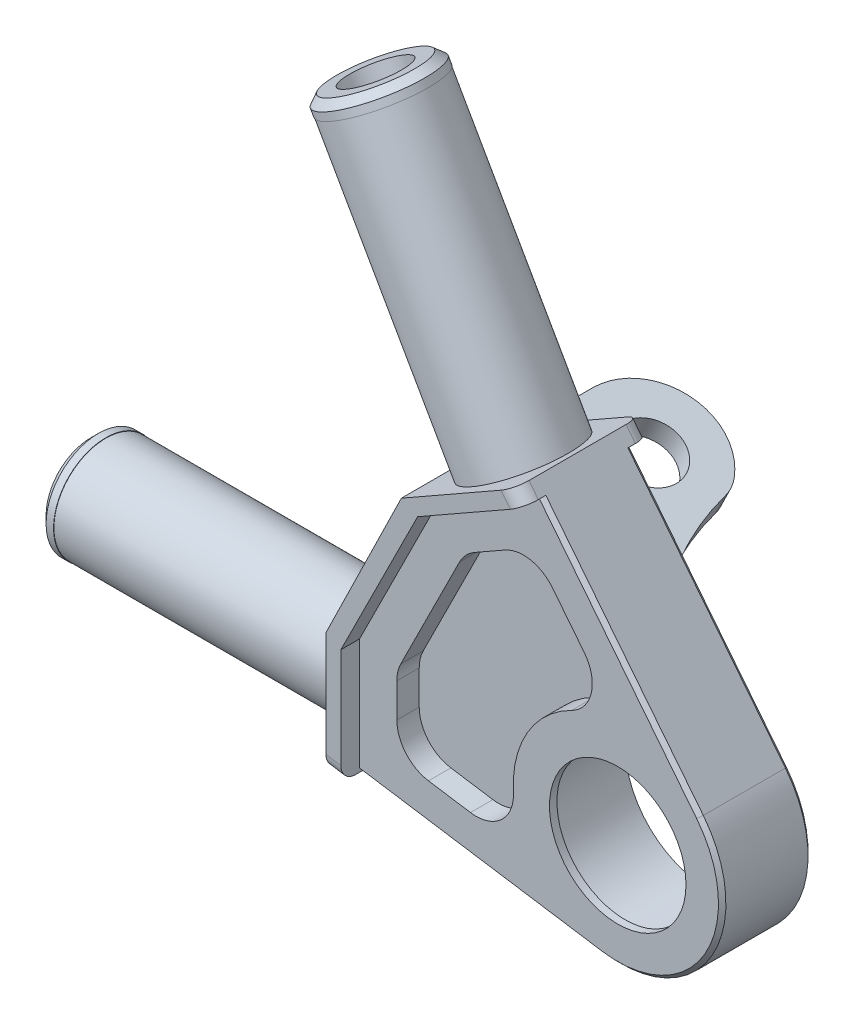
SolidWorks part; units mm, degrees
material "7075-T6 (SN)"
ref_plane "Płaszczyzna XY" through (0, 0, 0) normal (0, 0, 1) x (1, 0, 0)
ref_plane "Płaszczyzna XZ" through (0, 0, 0) normal (0, 1, 0) x (1, 0, 0)
ref_plane "Płaszczyzna YZ" through (0, 0, 0) normal (1, 0, 0) x (0, 0, -1)
sketch3d "Szkic 3D3"
  line L2 (-29.2958, 16.8586, -11.1226) -> (-29.2958, 16.8586, 0) construction
  line L3 (-9.7916, 7.3154, 0) -> (-29.2958, 16.8586, 0) construction
ref_plane "Płaszczyzna2" through (0.9966, 2.0369, 0) normal (0.4395, 0.8982, 0) x (0.8982, -0.4395, 0)
sketch "Szkic1" plane through (0, 0, 0) normal (0, 0, 1) x (1, 0, 0)
  line L0 (0, 0) -> (-69.9038, 0) construction
  line L1 (0, 0) -> (-41.2537, 72.4391) construction
  line L2 (-40, -8) -> (-2.1327, -13.8366)
  line L3 (-40, -8) -> (-40, 8)
  line L4 (-26.7466, 30.7997) -> (-12.8431, 38.7176)
  line L5 (-12.8431, 38.7176) -> (10.9681, 8.7006)
  line L9 (-26.7466, 30.7997) -> (-40, 8)
  circle A0 centre (0, 0) radius 11
  arc A1 (-2.1327, -13.8366) -> (10.9681, 8.7006) centre (0, 0) ccw
  dimension "D1" = 3
  dimension "D2" = 22
  dimension "D3" = 60.339
  dimension "D4" = 8
  dimension "D5" = 8
  dimension "D6" = 40
  dimension "D7" = 40
  dimension "D8" = 8
  dimension "D9" = 8
extrude "Dodanie-wyciągnięcie1" add sketch "Szkic1" along normal blind 12
sketch "Szkic4" plane through (0, 0, 12) normal (0, 0, 1) x (1, 0, 0)
  circle A0 centre (0, 0) radius 11.1475
  circle A1 centre (0, 0) radius 9.1475
  dimension "D1" = 2
extrude "Dodanie-wyciągnięcie2" add sketch "Szkic4" against normal blind 1
sketch "Szkic13" plane through (0.9966, 2.0369, 0) normal (0.4395, 0.8982, 0) x (0.8982, -0.4395, 0)
  line L0 (-36.2241, 11.1226) -> (-36.2241, 0)
  line L1 (-36.2241, 0) -> (-33.7241, 0)
  line L2 (-13.2241, 0) -> (-33.7241, 0)
  arc A0 (-20.3744, 15.3924) -> (-36.2241, 11.1226) centre (-27.7241, 11.1226) ccw
  arc A1 (-13.2241, 0) -> (-20.3744, 15.3924) centre (12.2627, 21.1964) cw
  circle A4 centre (-27.7241, 11.1226) radius 4
  dimension "D1" = 17
  dimension "D2" = 33.1492
  dimension "D3" = 23
  dimension "D4" = 15.3924
extrude "Dodanie-wyciągnięcie3" add sketch "Szkic13" along normal mid plane 23
ref_plane "Płaszczyzna3" through (0, 0, 6) normal (0, 0, -1) x (-1, 0, 0)
sketch "Szkic15" plane through (0, 0, 0) normal (0, 0, -1) x (-1, 0, 0)
  line L0 (12.8431, 38.7176) -> (26.7466, 30.7997)
  line L1 (26.7466, 30.7997) -> (40, 8)
  line L2 (40, 8) -> (40, -8)
  line L3 (12.0981, 37.4094) -> (11.8965, 37.5242)
  line L4 (12.8431, 38.7176) -> (11.8965, 37.5242)
  line L5 (40, -8) -> (38.4945, -8.232)
  line L7 (40, -8) -> (2.1327, -13.8366) construction
  line L8 (38.4945, 8) -> (38.4945, -8.232)
  line L10 (38.4945, 8) -> (26.0016, 29.4914)
  line L11 (26.0016, 29.4914) -> (12.0981, 37.4094)
  dimension "D1" = 1.5233
  dimension "D2" = 16
  dimension "D3" = 0.232
  dimension "D4" = 24.8587
  dimension "D5" = 16.232
extrude "Wytnij-wyciągnięcie1" cut sketch "Szkic15" against normal through all
sketch "Szkic16" plane through (0, 0, 0) normal (0, 0, -1) x (-1, 0, 0)
  line L1 (26.4872, 28.2872) -> (36.5957, 7.6276)
  line L2 (26.4872, 28.2872) -> (11.3895, 36.8852)
  line L3 (11.8965, 37.5242) -> (11.3895, 36.8852)
  line L4 (-10.9681, 8.7006) -> (11.8965, 37.5242) construction
  line L5 (11.8965, 37.5242) -> (26.0016, 29.4914)
  line L6 (26.0016, 29.4914) -> (38.4945, 8)
  line L7 (38.4945, 8) -> (38.4945, -8.232)
  line L10 (36.5957, 7.6276) -> (36.5957, -8.5247)
  line L11 (38.4945, -8.232) -> (36.5957, -8.5247)
  dimension "D1" = 1.9212
extrude "Wytnij-wyciągnięcie2" cut sketch "Szkic16" against normal through all
sketch "Szkic17" plane through (-32.5381, 15.9205, 0) normal (-0.8982, 0.4395, 0) x (0, 0, 1)
  line L2 (-27.8142, 10.7676) -> (-27.8142, -7.2324)
  line L4 (-27.8142, 10.7676) -> (0, 10.7676)
  line L5 (-27.8142, -7.2324) -> (0, -7.2324)
  line L6 (0, -7.2324) -> (2.5, -7.2324)
  line L7 (2.5, -7.2324) -> (2.5, 10.7676)
  line L8 (2.5, 10.7676) -> (0, 10.7676)
  line L10 (-11.1226, 13.7676) -> (0, 13.7676) construction
  line L11 (12, 13.7676) -> (12, -9.2324) construction
  dimension "D1" = 18
  dimension "D2" = 3
  dimension "D3" = 2.5
  dimension "D4" = 30.3142
  dimension "D5" = 9.5
extrude "Wytnij-wyciągnięcie3" cut sketch "Szkic17" against normal up to vertex (23 mm away)
sketch "Szkic18" plane through (0, 0, 6) normal (0, 0, -1) x (-1, 0, 0)
  line L0 (0, 0) -> (76.5957, 0) construction
  line L2 (76.5957, 0) -> (76.5957, -7)
  line L3 (76.5957, -7) -> (74.5957, -7)
  line L4 (74.5957, -7) -> (74.5957, -6.95)
  line L8 (74.5957, -6.95) -> (36.5957, -6.95)
  line L9 (36.5957, 7.6276) -> (36.5957, -8.5247) construction
  line L10 (36.5957, -6.95) -> (36.5957, 0)
  line L11 (36.5957, 0) -> (76.5957, 0)
  dimension "D1" = 40
  dimension "D2" = 7
  dimension "D3" = 2
  dimension "D4" = 6.95
revolve "Obrót1" add sketch "Szkic18" angle 360 about L0
sketch "Szkic19" plane through (0, 0, 6) normal (0, 0, -1) x (-1, 0, 0)
  line L0 (0, 0) -> (38.4457, 67.5085) construction
  line L1 (11.3895, 36.8852) -> (26.4872, 28.2872) construction
  line L2 (38.4457, 67.5085) -> (32.363, 70.9726)
  line L3 (32.363, 70.9726) -> (31.3732, 69.2347)
  line L4 (31.3732, 69.2347) -> (31.4167, 69.21)
  line L5 (31.4167, 69.21) -> (12.6116, 36.1893)
  line L6 (12.6116, 36.1893) -> (18.6509, 32.7499)
  line L7 (18.6509, 32.7499) -> (38.4457, 67.5085)
  dimension "D1" = 40
  dimension "D2" = 90
  dimension "D3" = 7
  dimension "D4" = 2
  dimension "D5" = 6.95
  dimension "D6" = 40
  dimension "D7" = 6.95
revolve "Obrót2" add sketch "Szkic19" angle 360 about L0
sketch "Szkic20" plane through (0, 0, 0) normal (0, 0, -1) x (-1, 0, 0)
  line L1 (36.5957, -8.5247) -> (34.5957, -8.833)
  line L2 (36.5957, -8.5247) -> (2.1327, -13.8366) construction
  line L4 (36.5957, 7.6276) -> (15.9361, -2.4809) construction
  line L5 (34.5957, 6.649) -> (36.5957, 7.6276)
  line L6 (26.4872, 28.2872) -> (11.3895, 36.8852)
  line L7 (11.3895, 36.8852) -> (10.1319, 35.2998)
  line L8 (-10.9681, 8.7006) -> (11.3895, 36.8852) construction
  line L9 (10.1319, 35.2998) -> (24.3134, 27.2235)
  line L10 (26.4872, 28.2872) -> (12.2503, 21.3212) construction
  line L11 (24.3134, 27.2235) -> (26.4872, 28.2872)
  line L12 (36.5957, 7.6276) -> (36.5957, -8.5247)
  line L13 (34.5957, -8.833) -> (34.5957, 6.649)
  dimension "D1" = 2
  dimension "D2" = 2
extrude "Dodanie-wyciągnięcie4" add sketch "Szkic20" along normal blind 2.5 and the other way blind 14.5
sketch "Szkic21" plane through (0, 0, 12) normal (0, 0, 1) x (1, 0, 0)
  line L3 (-24.3134, 27.2235) -> (-26.4872, 28.2872)
  line L4 (-24.3134, 27.2235) -> (-34.5957, 6.649)
  line L5 (-34.5957, 6.649) -> (-36.5957, 7.6276)
  line L6 (-36.5957, 7.6276) -> (-26.4872, 28.2872)
extrude "Dodanie-wyciągnięcie5" add sketch "Szkic21" along normal blind 2.5
hole_wizard "Otwory ustalające Ø8.0mm1" positions "Szkic 3D4" profile "Szkic22" hole size "Ø8.0" standard "ISO"
sketch3d "Szkic 3D4"
  line L0 (-76.5957, 0, 6) -> (-74.5957, 0, 6) construction
  point P0 (-76.5957, 0, 6)
sketch "Szkic22" plane through (-76.5957, 0, 6) normal (0, 1, 0) x (0, 0, 1)
  line L0 (0, 0) -> (0, 42.4034)
  line L1 (0, 42.4034) -> (4, 40)
  line L2 (4, 40) -> (4, 0)
  line L5 (4, 0) -> (0, 0)
  line L10 (0, 42.4034) -> (-4, 40) construction
  line L11 (0, -6.35) -> (0, 107.95) construction
  dimension "Średnica otworu" = 8
  dimension "Głębokość otworu" = 40
  dimension "Kąt wiertła" = 118
hole_wizard "Otwory ustalające Ø8.0mm2" positions "Szkic 3D5" profile "Szkic23" hole size "Ø8.0" standard "ISO"
sketch3d "Szkic 3D5"
  line L0 (-38.4457, 67.5085, 6) -> (-37.456, 65.7706, 6) construction
  point P0 (-38.4457, 67.5085, 6)
sketch "Szkic23" plane through (-38.4457, 67.5085, 6) normal (0, 0, 1) x (-0.869, -0.4949, 0)
  line L0 (0, 0) -> (0, 42.4034)
  line L1 (0, 42.4034) -> (4, 40)
  line L2 (4, 40) -> (4, 0)
  line L5 (4, 0) -> (0, 0)
  line L10 (0, 42.4034) -> (-4, 40) construction
  line L11 (0, -6.35) -> (0, 107.95) construction
  dimension "Średnica otworu" = 8
  dimension "Głębokość otworu" = 40
  dimension "Kąt wiertła" = 118
chamfer "Sfazowanie1" distance 1 angle 45 2 edges at (-32.363, 70.9726, 6) (-76.5957, 0, -1)
fillet "Zaokrąglenie2" radius 2 4 edges at (-10.7607, 36.0925, -2.5) (-10.7607, 36.0925, 14.5) (-35.5957, -8.6788, 14.5) (-35.5957, -8.6788, -2.5)
fillet "Zaokrąglenie3" radius 5 4 edges at (-24.3134, 27.2235, -1.25) (-15.0571, -0.6844, 1.25) (-7.1461, 15.4839, 1.25) (-34.5957, 6.649, -1.25)
chamfer "Sfazowanie2" distance 0.5 angle 45 6 edges at (-18.3642, -11.3348, 0) (-18.3642, -11.3348, 12) (12.1036, -7.0358, 0) (12.1036, -7.0358, 12) (0.4181, 22.0002, 12) (0.4181, 22.0002, 0)
fillet "Zaokrąglenie4" radius 0.3 1 edges at (11, 0, 11)
sketch "Szkic24" plane through (6.0509, 12.3667, 0) normal (0.4395, 0.8982, 0) x (0.8982, -0.4395, 0)
  line L0 (-27.7241, 11.1226) -> (-3.3355, 11.1226) construction
  line L2 (-27.7241, 11.1226) -> (-19.5533, -3.0985) construction
  dimension "D1" = 60.12
fillet "Zaokrąglenie5" radius 5 2 edges at (-21.9193, 1.5599, -15.3924) (-12.9096, 19.9739, -15.3924)
sketch "Szkic29" plane through (0, 0, 12) normal (0, 0, 1) x (1, 0, 0)
  line L0 (-29.5957, -4.5446) -> (-29.5957, 5.4692)
  line L1 (-20.5196, 23.6301) -> (-29.5957, 5.4692)
  line L2 (-20.5196, 23.6301) -> (-11.384, 28.8328)
  line L3 (-34.5957, -8.3271) -> (-34.5957, 6.649) construction
  line L5 (-24.3134, 27.2235) -> (-10.5715, 35.0495) construction
  line L10 (-34.5957, 6.649) -> (-24.3134, 27.2235) construction
  line L12 (-29.5957, -4.5446) -> (-11.9697, -7.2614)
  line L13 (-2.1327, -13.8366) -> (-34.5957, -8.833) construction
  line L16 (-11.384, 28.8328) -> (0.3864, 13.9947)
  line L17 (-10.1319, 35.2998) -> (10.9681, 8.7006) construction
  arc A0 (0.3864, 13.9947) -> (-11.9697, -7.2614) centre (0, 0) ccw
  dimension "D4" = 28
  dimension "D1" = 5
  dimension "D2" = 5
  dimension "D3" = 5
  dimension "D5" = 5
  dimension "D6" = 5
extrude "Wytnij-wyciągnięcie4" cut sketch "Szkic29" against normal blind 3
fillet "Zaokrąglenie11" radius 5 6 edges at (-11.9697, -7.2614, 10.5) (0.3864, 13.9947, 10.5) (-11.384, 28.8328, 10.5) (-29.5957, -4.5446, 10.5) (-29.5957, 5.4692, 10.5) (-20.5196, 23.6301, 10.5)
